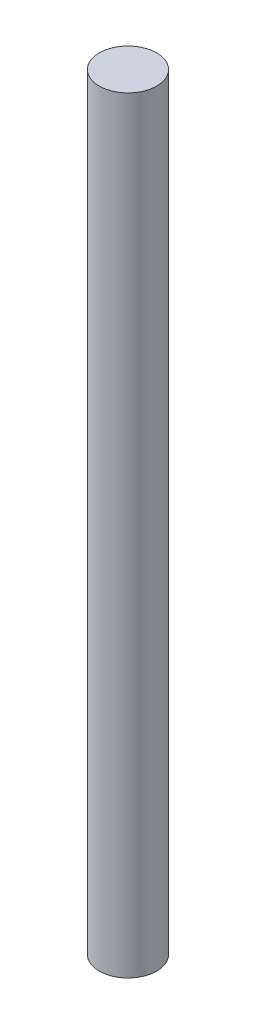
SolidWorks part; units mm, degrees
ref_plane "Front Plane" through (0, 0, 0) normal (0, 0, 1) x (1, 0, 0)
ref_plane "Top Plane" through (0, 0, 0) normal (0, 1, 0) x (1, 0, 0)
ref_plane "Right Plane" through (0, 0, 0) normal (1, 0, 0) x (0, 0, -1)
sketch "Sketch1" plane through (0, 0, 0) normal (0, 1, 0) x (1, 0, 0)
  circle A0 centre (0, 0) radius 1.5
  dimension "D1" = 3
extrude "Boss-Extrude1" add sketch "Sketch1" along normal blind 40
